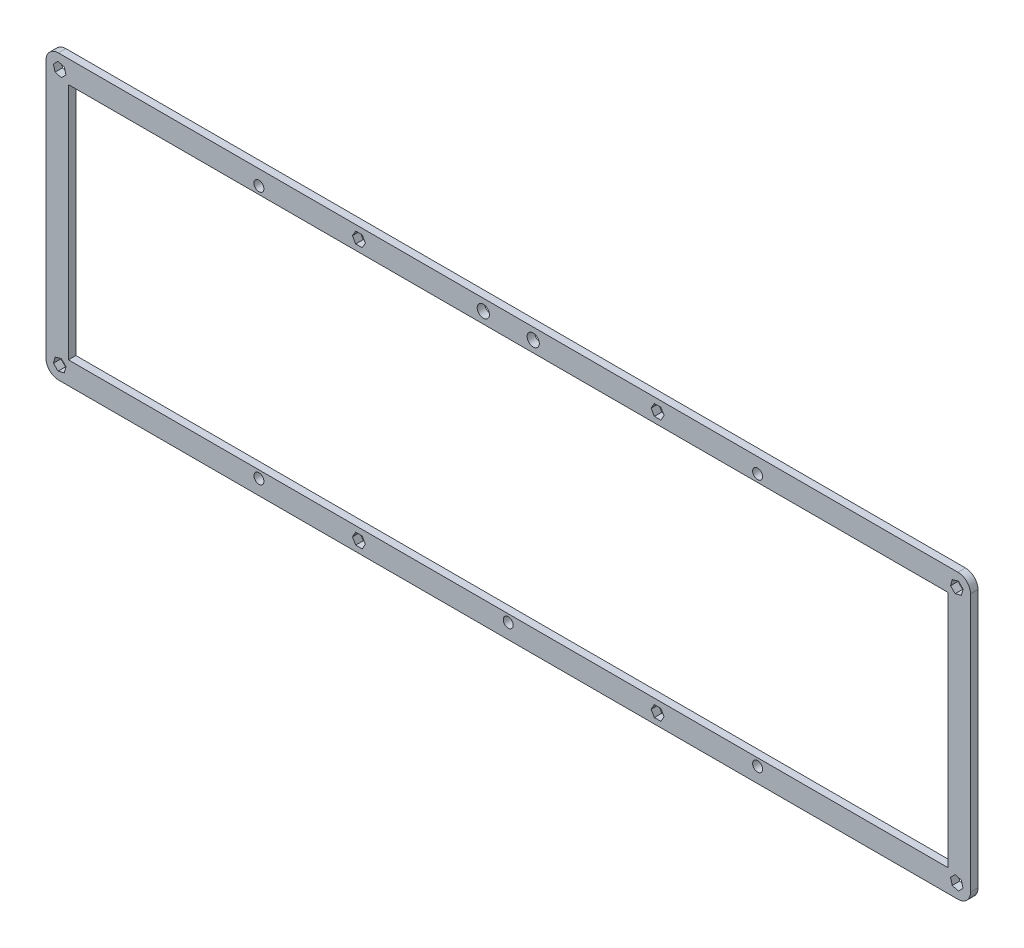
SolidWorks part; units mm, degrees
ref_plane "Front Plane" through (0, 0, 0) normal (0, 0, 1) x (1, 0, 0)
ref_plane "Top Plane" through (0, 0, 0) normal (0, 1, 0) x (1, 0, 0)
ref_plane "Right Plane" through (0, 0, 0) normal (1, 0, 0) x (0, 0, -1)
sketch "Model" plane through (0, 0, 0) normal (0, 0, 1) x (1, 0, 0)
  line L0 (0, 108.6) -> (0, 5)
  line L1 (9, 104.6) -> (9, 9)
  line L2 (365.775, 0) -> (5, 0)
  line L3 (361.775, 9) -> (9, 9)
  line L4 (370.775, 108.6) -> (370.775, 5)
  line L5 (361.775, 104.6) -> (361.775, 9)
  line L6 (365.775, 113.6) -> (5, 113.6)
  line L7 (361.775, 104.6) -> (9, 104.6)
  line L8 (365.9474, 110.6095) -> (367.7845, 108.7724)
  line L9 (367.7845, 108.7724) -> (367.1121, 106.2629)
  line L10 (367.1121, 106.2629) -> (364.6026, 105.5905)
  line L11 (364.6026, 105.5905) -> (362.7655, 107.4276)
  line L12 (362.7655, 107.4276) -> (363.4379, 109.9371)
  line L13 (363.4379, 109.9371) -> (365.9474, 110.6095)
  line L14 (4.8276, 110.6095) -> (2.9905, 108.7724)
  line L15 (2.9905, 108.7724) -> (3.6629, 106.2629)
  line L16 (3.6629, 106.2629) -> (6.1724, 105.5905)
  line L17 (6.1724, 105.5905) -> (8.0095, 107.4276)
  line L18 (8.0095, 107.4276) -> (7.3371, 109.9371)
  line L19 (7.3371, 109.9371) -> (4.8276, 110.6095)
  line L20 (365.9474, 2.9905) -> (367.7845, 4.8276)
  line L21 (367.7845, 4.8276) -> (367.1121, 7.3371)
  line L22 (367.1121, 7.3371) -> (364.6026, 8.0095)
  line L23 (364.6026, 8.0095) -> (362.7655, 6.1724)
  line L24 (362.7655, 6.1724) -> (363.4379, 3.6629)
  line L25 (363.4379, 3.6629) -> (365.9474, 2.9905)
  line L26 (4.8276, 2.9905) -> (2.9905, 4.8276)
  line L27 (2.9905, 4.8276) -> (3.6629, 7.3371)
  line L28 (3.6629, 7.3371) -> (6.1724, 8.0095)
  line L29 (6.1724, 8.0095) -> (8.0095, 6.1724)
  line L30 (8.0095, 6.1724) -> (7.3371, 3.6629)
  line L31 (7.3371, 3.6629) -> (4.8276, 2.9905)
  line L32 (0, 5) -> (0, 0)
  line L33 (0, 0) -> (5, 0)
  line L34 (126.799, 2.25) -> (124.201, 2.25)
  line L35 (124.201, 2.25) -> (122.9019, 4.5)
  line L36 (122.9019, 4.5) -> (124.201, 6.75)
  line L37 (124.201, 6.75) -> (126.799, 6.75)
  line L38 (126.799, 6.75) -> (128.0981, 4.5)
  line L39 (128.0981, 4.5) -> (126.799, 2.25)
  line L40 (126.799, 111.35) -> (124.201, 111.35)
  line L41 (124.201, 111.35) -> (122.9019, 109.1)
  line L42 (122.9019, 109.1) -> (124.201, 106.85)
  line L43 (124.201, 106.85) -> (126.799, 106.85)
  line L44 (126.799, 106.85) -> (128.0981, 109.1)
  line L45 (128.0981, 109.1) -> (126.799, 111.35)
  line L46 (243.976, 2.25) -> (246.574, 2.25)
  line L47 (246.574, 2.25) -> (247.8731, 4.5)
  line L48 (247.8731, 4.5) -> (246.574, 6.75)
  line L49 (246.574, 6.75) -> (243.976, 6.75)
  line L50 (243.976, 6.75) -> (242.6769, 4.5)
  line L51 (242.6769, 4.5) -> (243.976, 2.25)
  line L52 (243.976, 111.35) -> (246.574, 111.35)
  line L53 (246.574, 111.35) -> (247.8731, 109.1)
  line L54 (247.8731, 109.1) -> (246.574, 106.85)
  line L55 (246.574, 106.85) -> (243.976, 106.85)
  line L56 (243.976, 106.85) -> (242.6769, 109.1)
  line L57 (242.6769, 109.1) -> (243.976, 111.35)
  arc A0 (365.775, 0) -> (370.775, 5) centre (365.775, 5) ccw
  arc A1 (370.775, 108.6) -> (365.775, 113.6) centre (365.775, 108.6) ccw
  arc A2 (0, 5) -> (5, 0) centre (5, 5) ccw
  arc A3 (5, 113.6) -> (0, 108.6) centre (5, 108.6) ccw
  circle A4 centre (85.3875, 107.6) radius 2
  circle A5 centre (285.3875, 107.6) radius 2
  circle A6 centre (85.3875, 6) radius 2
  circle A7 centre (185.3875, 6) radius 2
  circle A8 centre (285.3875, 6) radius 2
  circle A9 centre (175.3875, 109.1) radius 2.45
  circle A10 centre (195.3875, 109.1) radius 2.45
  dimension "D2" = 4
  dimension "D3" = 4
  dimension "D4" = 4
  dimension "D5" = 4
  dimension "D6" = 4
  dimension "D7" = 4.9
  dimension "D8" = 4.9
  dimension "D1" = 113.6
extrude "Boss-Extrude1" add sketch "Model" along normal blind 3 contours L6 A3 L0 A2 L2 A0 L4 A1 A10 A9 A8 A7 A6 A5 A4 L56 L57 L52 L53 L54 L55 L38 L39 L34 L35 L36 L37 L30 L31 L26 L27 L28 L29 L12 L13 L8 L9 L10 L11
equation "\"A\" =4"
equation "\"D2@Model\"=\"A\""
equation "\"D3@Model\"=\"A\""
equation "\"D4@Model\"=\"A\""
equation "\"D5@Model\"=\"A\""
equation "\"D6@Model\"=\"A\""
equation "\"D7@Model\"=\"B\""
equation "\"D8@Model\"=\"B\""
equation "\"B\"= 4.9"
